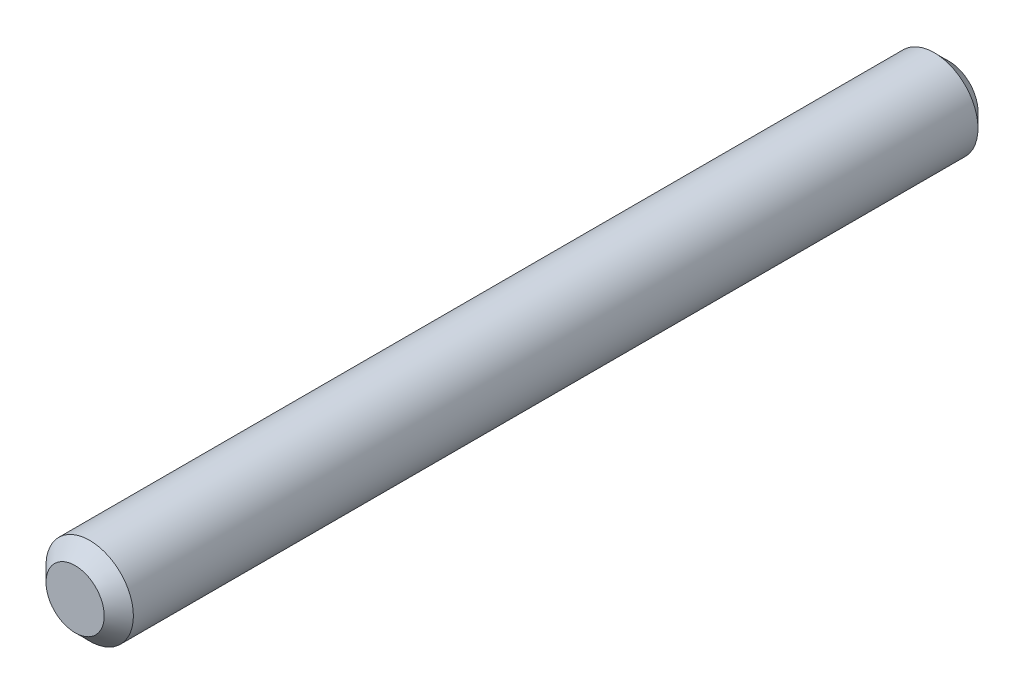
SolidWorks part; units mm, degrees
material "Plain Carbon Steel"
ref_plane "Front Plane" through (0, 0, 0) normal (0, 0, 1) x (1, 0, 0)
ref_plane "Top Plane" through (0, 0, 0) normal (0, 1, 0) x (1, 0, 0)
ref_plane "Right Plane" through (0, 0, 0) normal (1, 0, 0) x (0, 0, -1)
sketch "Sketch1" plane through (0, 0, 0) normal (0, 0, 1) x (1, 0, 0)
  circle A0 centre (0, 0) radius 3
  dimension "D1" = 6
extrude "Boss-Extrude1" add sketch "Sketch1" along normal mid plane 60
chamfer "Chamfer1" distance 1 angle 45 1 edges at (3, 0, 30)
cosmetic thread "Cosmetic Thread1" parameters "D1"=10, "D2"=4.891
chamfer "Chamfer2" distance 1 angle 45 1 edges at (3, 0, -30)
cosmetic thread "Cosmetic Thread2" parameters "D1"=10, "D2"=4.891
